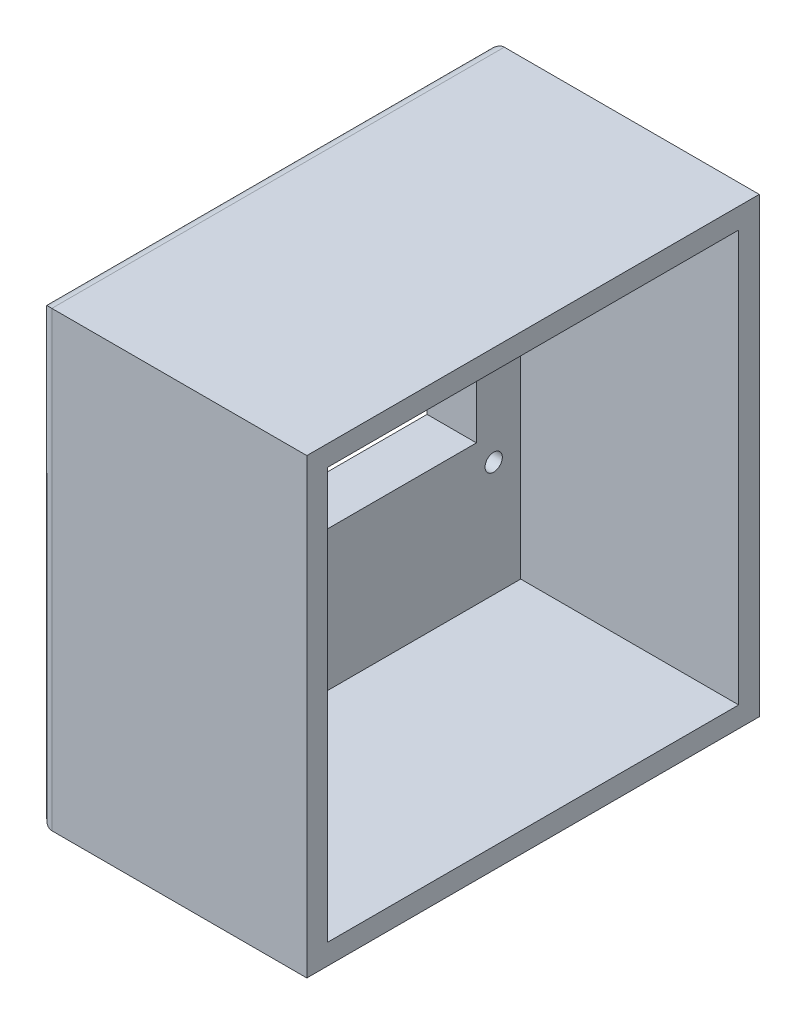
SolidWorks part; units mm, degrees
ref_plane "Front Plane" through (0, 0, 0) normal (0, 0, 1) x (1, 0, 0)
ref_plane "Top Plane" through (0, 0, 0) normal (0, 1, 0) x (1, 0, 0)
ref_plane "Right Plane" through (0, 0, 0) normal (1, 0, 0) x (0, 0, -1)
sketch "Esboço1" plane through (0, 0, 0) normal (1, 0, 0) x (0, 0, -1)
  line L20 (-364.4545, 439.2408) -> (-464.4545, 439.2408)
  line L21 (-364.4545, 439.2408) -> (-364.4545, 339.2408)
  line L22 (-364.4545, 339.2408) -> (-464.4545, 339.2408)
  line L23 (-464.4545, 439.2408) -> (-464.4545, 339.2408)
  circle A1 centre (-371.078, 432.9462) radius 2.1
  circle A3 centre (-371.0241, 367.1462) radius 2.1
  circle A5 centre (-458.878, 432.8742) radius 2.1
  circle A7 centre (-458.824, 367.0743) radius 2.1
  circle A9 centre (-451.1653, 356.4871) radius 3.5
  circle A11 centre (-418.1654, 356.5084) radius 3.4
  dimension "D1" = 100
  dimension "D2" = 100
extrude "Ressalto-extrusão1" add sketch "Esboço1" along normal blind 12
sketch "Esboço2" plane through (0, 0, 0) normal (-1, 0, 0) x (0, 0, 1)
  line L1 (375.2209, 426.2989) -> (455.2209, 426.2989)
  line L2 (375.2209, 426.2989) -> (375.2209, 373.2989)
  line L3 (375.2209, 373.2989) -> (455.2209, 373.2989)
  line L4 (455.2209, 426.2989) -> (455.2209, 373.2989)
  dimension "D1" = 80
  dimension "D2" = 53
extrude "Corte-extrusão1" cut sketch "Esboço2" against normal blind 12
sketch "Esboço3" plane through (0, 0, 0) normal (-1, 0, 0) x (0, 0, 1)
  line L4 (364.4545, 439.2408) -> (364.4545, 339.2408)
  line L5 (364.4545, 339.2408) -> (464.4545, 339.2408)
  line L6 (464.4545, 339.2408) -> (464.4545, 439.2408)
  line L7 (464.4545, 439.2408) -> (364.4545, 439.2408)
  line L12 (359.4545, 444.2408) -> (359.4545, 334.2408)
  line L13 (359.4545, 334.2408) -> (469.4545, 334.2408)
  line L14 (469.4545, 334.2408) -> (469.4545, 444.2408)
  line L15 (469.4545, 444.2408) -> (359.4545, 444.2408)
extrude "Ressalto-extrusão2" add sketch "Esboço3" against normal blind 65
fillet "Filete1" radius 3 4 edges at (0, 334.2408, 414.4545) (0, 389.2408, 359.4545) (0, 444.2408, 414.4545) (0, 389.2408, 469.4545)
